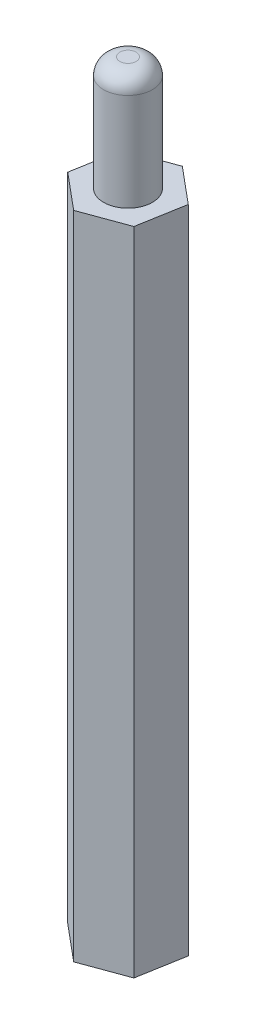
SolidWorks part; units mm, degrees
ref_plane "Front Plane" through (0, 0, 0) normal (0, 0, 1) x (1, 0, 0)
ref_plane "Top Plane" through (0, 0, 0) normal (0, 1, 0) x (1, 0, 0)
ref_plane "Right Plane" through (0, 0, 0) normal (1, 0, 0) x (0, 0, -1)
sketch "Sketch1" plane through (0, 0, 0) normal (0, 1, 0) x (1, 0, 0)
  line L1 (2.2148, -1.8515) -> (2.7108, 0.9924)
  line L2 (2.7108, 0.9924) -> (0.496, 2.8438)
  line L3 (0.496, 2.8438) -> (-2.2148, 1.8515)
  line L4 (-2.2148, 1.8515) -> (-2.7108, -0.9924)
  line L5 (-2.7108, -0.9924) -> (-0.496, -2.8438)
  line L6 (-0.496, -2.8438) -> (2.2148, -1.8515)
  circle A0 centre (0, 0) radius 2.5 construction
  dimension "D1" = 5
extrude "Boss-Extrude1" add sketch "Sketch1" along normal blind 40
sketch "Sketch2" plane through (0, 40, 0) normal (0, 1, 0) x (1, 0, 0)
  circle A0 centre (0, 0) radius 1.5
  dimension "D1" = 3
extrude "Boss-Extrude2" add sketch "Sketch2" along normal blind 7
sketch "Sketch3" plane through (0, 0, 0) normal (0, -1, 0) x (1, 0, 0)
  circle A0 centre (0, 0) radius 1.5
extrude "Cut-Extrude1" cut sketch "Sketch3" against normal blind 7
fillet "Fillet1" radius 1 1 edges at (0, 47, 1.5)
